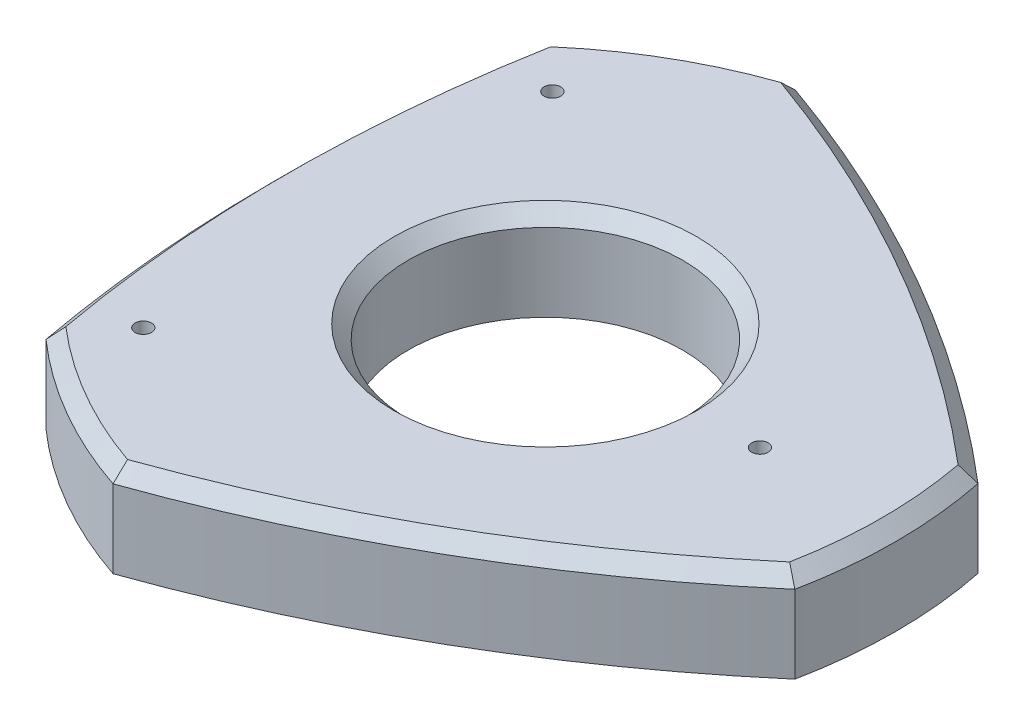
SolidWorks part; units mm, degrees
ref_plane "Front Plane" through (0, 0, 0) normal (0, 0, 1) x (1, 0, 0)
ref_plane "Top Plane" through (0, 0, 0) normal (0, 1, 0) x (1, 0, 0)
ref_plane "Right Plane" through (0, 0, 0) normal (1, 0, 0) x (0, 0, -1)
sketch "Sketch1" plane through (0, 0, 0) normal (0, 1, 0) x (1, 0, 0)
  line L0 (-54.5596, 54.5) -> (-19.9186, 74.5) construction
  line L1 (109.1192, 0) -> (-54.5596, 94.5) construction
  line L2 (-54.5596, 94.5) -> (-54.5596, -94.5) construction
  line L3 (-54.5596, -94.5) -> (109.1192, 0) construction
  line L4 (74.4782, 20) -> (74.4782, -20) construction
  line L5 (-19.9186, -74.5) -> (-54.5596, -54.5) construction
  line L6 (-59.5596, 0) -> (-54.5596, 0) construction
  line L7 (-38.2391, 66.2321) -> (-37.2391, 64.5) construction
  line L8 (29.7798, 51.5801) -> (27.2798, 47.25) construction
  line L9 (76.4782, 0) -> (74.4782, 0) construction
  line L10 (29.7798, -51.5801) -> (27.2798, -47.25) construction
  line L11 (-38.2391, -66.2321) -> (-37.2391, -64.5) construction
  line L18 (-54.5596, 94.5) -> (0, 0) construction
  line L19 (0, 0) -> (-54.5596, -94.5) construction
  line L20 (0, 0) -> (109.1192, 0) construction
  circle A0 centre (0, 0) radius 30
  arc A2 (-54.5596, 54.5) -> (-54.5596, -54.5) centre (239.9654, 0) ccw
  arc A3 (-19.9186, 74.5) -> (74.4782, 20) centre (-119.9827, -207.8161) cw
  arc A5 (74.4782, -20) -> (-19.9186, -74.5) centre (-119.9827, 207.8161) cw
  arc A7 (-54.5596, 54.5) -> (-19.9186, 74.5) centre (12.2609, -21.2365) cw
  arc A8 (-54.5596, -54.5) -> (-19.9186, -74.5) centre (12.2609, 21.2365) ccw
  arc A9 (74.4782, -20) -> (74.4782, 20) centre (-24.5218, 0) ccw
  spline S0 degree 1 poles (-54.5596, 54.5) (-19.9186, 74.5) knots 0 0 1 1 construction
  dimension "D1" = 60
  dimension "D2" = 109
  dimension "D4" = 5
  dimension "D3" = 40
  dimension "D5" = 2
extrude "Boss-Extrude1" add sketch "Sketch1" along normal blind 20
chamfer "Chamfer1" distance 3 angle 45 7 edges at (0, 20, 30) (29.7798, 20, -51.5801) (76.4782, 20, 0) (29.7798, 20, 51.5801) (-38.2391, 20, 66.2321) (-59.5596, 20, 0) (-38.2391, 20, -66.2321)
hole_wizard "M3 Clearance Hole1" positions "Sketch2" profile "Sketch3" hole size "M3" standard "ANSI Metric" end condition through all
sketch "Sketch2" plane through (0, 20, 0) normal (0, 1, 0) x (1, 0, 0)
  circle A1 centre (-9.2312, 0) radius 56.0858
  point P25 (-43.1454, 44.6703)
  point P27 (-43.1454, -44.6703)
  point P29 (46.8546, 0)
  point P34 (0, 0)
  point P38 (-9.2312, 0)
  dimension "D1" = 90
sketch "Sketch3" plane through (0, 20, 0) normal (1, 0, 0) x (0, 0, 1)
  line L0 (0, 0) -> (0, 20)
  line L1 (0, 20) -> (1.8, 20)
  line L2 (1.8, 20) -> (1.8, 0)
  line L5 (1.8, 0) -> (0, 0)
  line L11 (0, -6.35) -> (0, 107.95) construction
  dimension "Thru Hole Dia." = 3.6
  dimension "Thru Hole Depth" = 20
